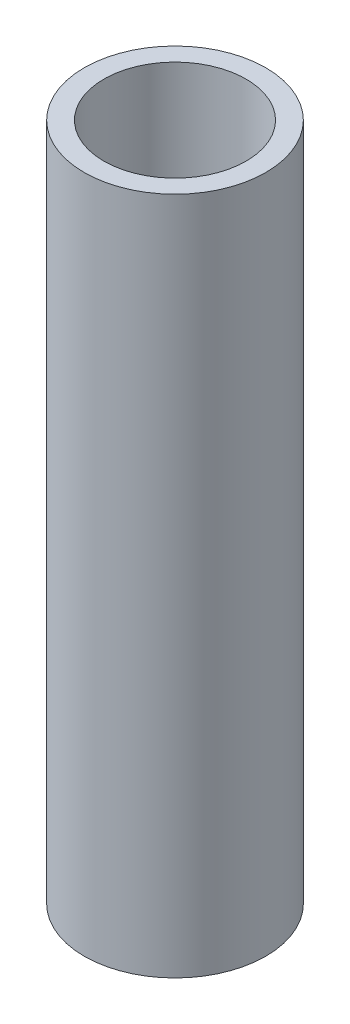
SolidWorks part; units mm, degrees
material "Glass"
ref_plane "Front Plane" through (0, 0, 0) normal (0, 0, 1) x (1, 0, 0)
ref_plane "Top Plane" through (0, 0, 0) normal (0, 1, 0) x (1, 0, 0)
ref_plane "Right Plane" through (0, 0, 0) normal (1, 0, 0) x (0, 0, -1)
sketch "Sketch1" plane through (0, 0, 0) normal (0, 1, 0) x (1, 0, 0)
  circle A0 centre (0, 0) radius 13.3731
  circle A1 centre (0, 0) radius 10.4775
  dimension "D1" = 26.7462
  dimension "D2" = 2.8956
extrude "Boss-Extrude1" add sketch "Sketch1" along normal blind 99.9998
